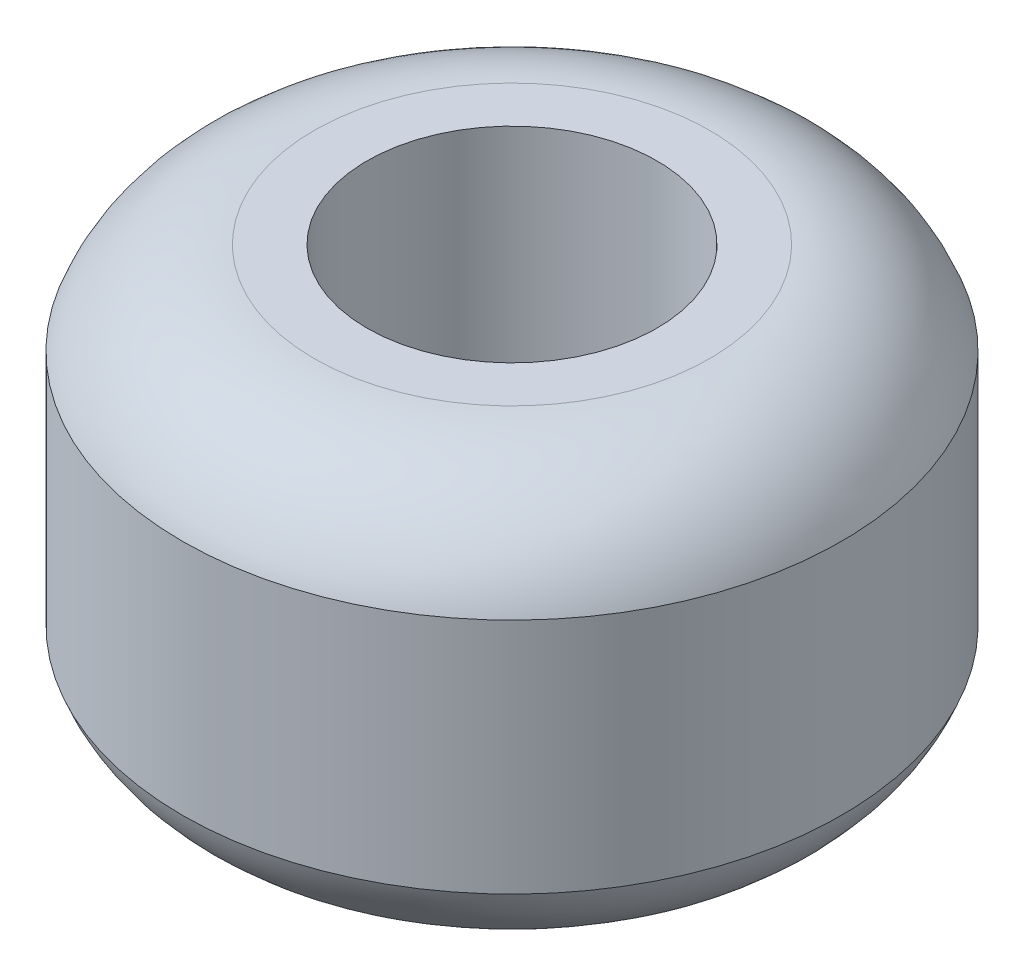
SolidWorks part; units mm, degrees
ref_plane "Front Plane" through (0, 0, 0) normal (0, 0, 1) x (1, 0, 0)
ref_plane "Top Plane" through (0, 0, 0) normal (0, 1, 0) x (1, 0, 0)
ref_plane "Right Plane" through (0, 0, 0) normal (1, 0, 0) x (0, 0, -1)
sketch "Sketch1" plane through (0, 0, 0) normal (0, 0, 1) x (1, 0, 0)
  line L0 (11, 16) -> (11, -16)
  line L1 (11, -16) -> (15, -16)
  line L2 (25, -9) -> (25, 9)
  line L3 (25, 0) -> (11, 0) construction
  line L4 (11, 16) -> (15, 16)
  line L5 (0, 0) -> (0, -19.2635) construction
  arc A0 (15, -16) -> (25, -9) centre (15, -5.3571) ccw
  arc A1 (15, 16) -> (25, 9) centre (15, 5.3571) cw
  dimension "D1" = 25
  dimension "D2" = 11
  dimension "D3" = 16
  dimension "D4" = 4
  dimension "D5" = 7
revolve "Revolve1" add sketch "Sketch1" angle 360 about L5
